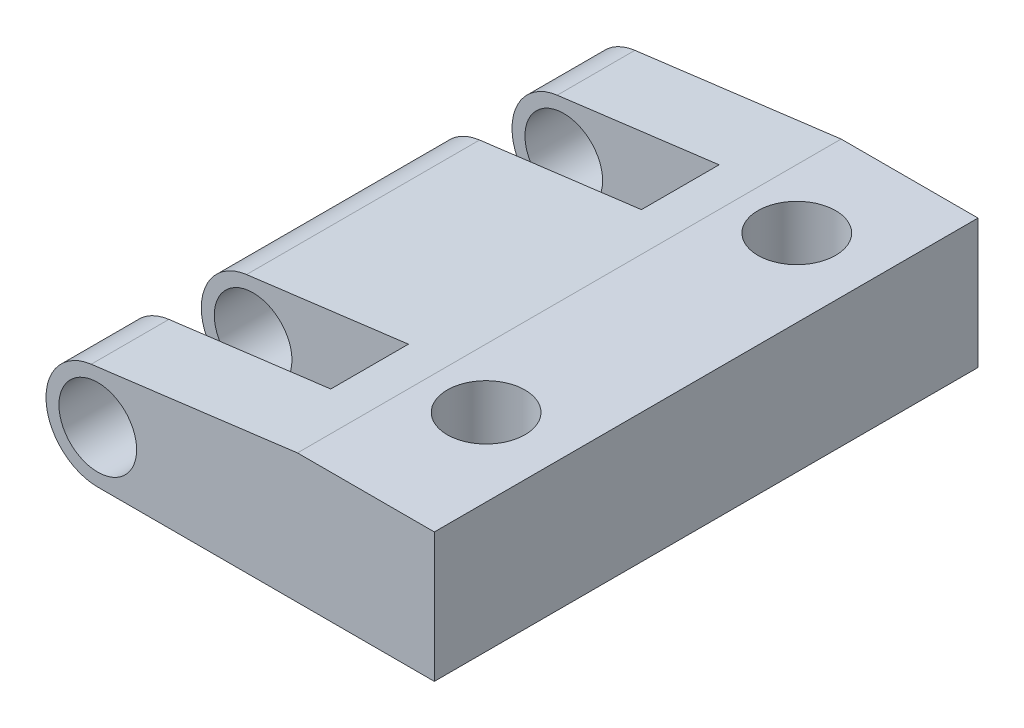
SolidWorks part; units mm, degrees
ref_plane "前视基准面" through (0, 0, 0) normal (0, 0, 1) x (1, 0, 0)
ref_plane "上视基准面" through (0, 0, 0) normal (0, 1, 0) x (1, 0, 0)
ref_plane "右视基准面" through (0, 0, 0) normal (1, 0, 0) x (0, 0, -1)
sketch "草图1" plane through (0, 0, 0) normal (0, 0, 1) x (1, 0, 0)
  line L0 (-1.9362, 5) -> (3.3502, 5)
  line L2 (3.3502, 5) -> (3.3502, 0)
  line L3 (55, 0) -> (-55, 0) construction
  line L4 (3.3502, 0) -> (0, 0)
  line L5 (0, 0) -> (-9.6498, 0)
  line L6 (-1.9362, 5) -> (-9.9028, 3.9839)
  arc A0 (-9.9028, 3.9839) -> (-9.6498, 0) centre (-9.6498, 2) ccw
  circle A1 centre (-9.6498, 2) radius 1.5
  point P12 (3.3502, 2.5)
  dimension "D2" = 2
  dimension "D4" = 3
  dimension "D1" = 5
  dimension "D3" = 13
extrude "凸台-拉伸1" add sketch "草图1" along normal blind 21
sketch "草图3" plane through (0, 0, 0) normal (0, 1, 0) x (1, 0, 0)
  line L0 (-11.6498, 0) -> (-11.6498, -21) construction
  line L1 (-3.6498, -3) -> (-11.6498, -3)
  line L2 (-3.6498, -3) -> (-3.6498, -6)
  line L3 (-3.6498, -6) -> (-11.6498, -6)
  line L4 (-11.6498, -3) -> (-11.6498, -6)
  line L5 (-3.6498, -15) -> (-11.6498, -15)
  line L6 (-3.6498, -15) -> (-3.6498, -18)
  line L7 (-3.6498, -18) -> (-11.6498, -18)
  line L8 (-11.6498, -15) -> (-11.6498, -18)
  line L9 (-2.75, 0) -> (2.75, 0) construction
  line L10 (-11.6498, -21) -> (-9.6498, -21) construction
  dimension "D1" = 3
  dimension "D2" = 3
  dimension "D3" = 8
  dimension "D4" = 8
  dimension "D5" = 3
  dimension "D6" = 3
extrude "切除-拉伸1" cut sketch "草图3" along normal through all
sketch "草图4" plane through (0, 5, 0) normal (0, 1, 0) x (1, 0, 0)
  line L0 (3.3502, -21) -> (-1.9362, -21) construction
  line L2 (3.3502, -21) -> (3.3502, 0) construction
  circle A0 centre (0.3502, -4) radius 1.5
  circle A1 centre (0.3502, -16) radius 1.5
  dimension "D1" = 3
  dimension "D2" = 3
  dimension "D3" = 12
  dimension "D4" = 5
  dimension "D5" = 3
extrude "切除-拉伸2" cut sketch "草图4" against normal blind 21
